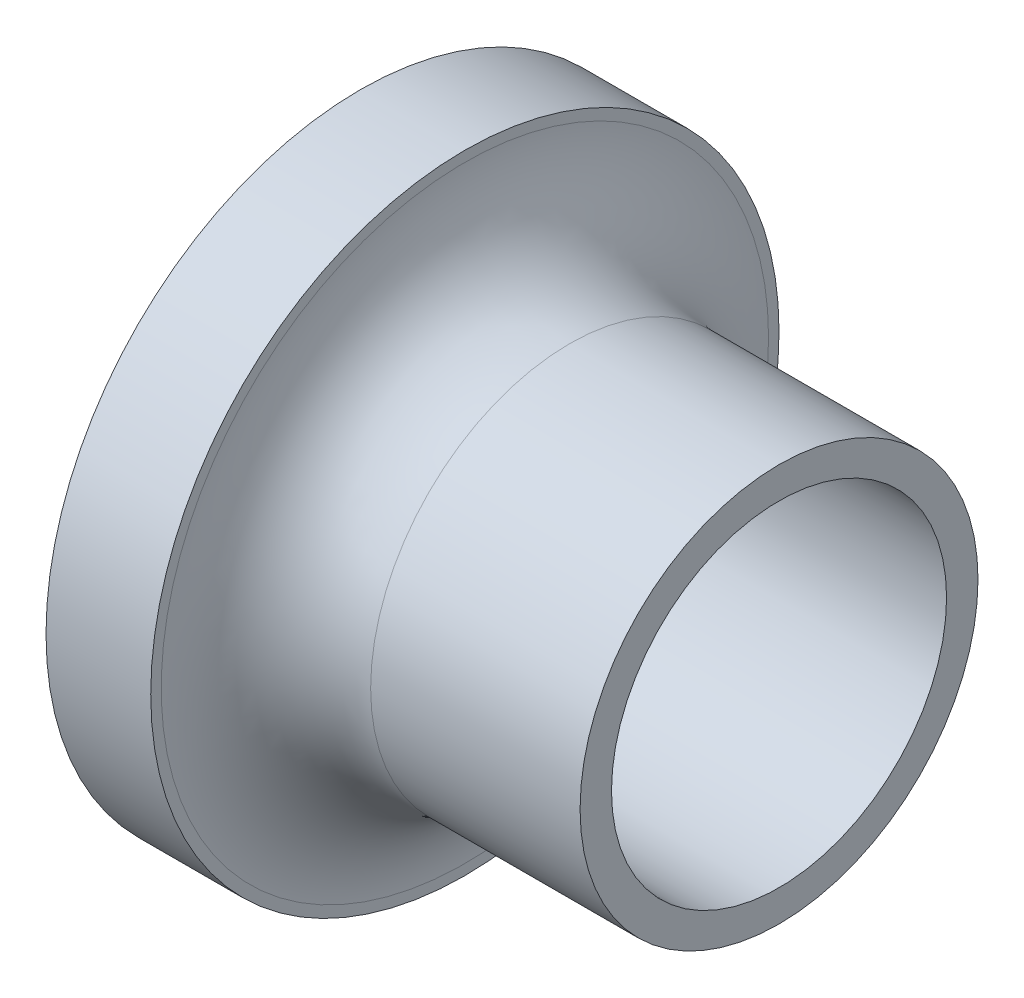
SolidWorks part; units mm, degrees
ref_plane "Piano frontale" through (0, 0, 0) normal (0, 0, 1) x (1, 0, 0)
ref_plane "Piano superiore" through (0, 0, 0) normal (0, 1, 0) x (1, 0, 0)
ref_plane "Piano destro" through (0, 0, 0) normal (1, 0, 0) x (0, 0, -1)
sketch "Schizzo1" plane through (0, 0, 0) normal (1, 0, 0) x (0, 0, -1)
  circle A0 centre (0, 0) radius 9.5
  circle A1 centre (0, 0) radius 8
  dimension "D1" = 16
  dimension "D2" = 19
extrude "Estrusione-Estrusione1" add sketch "Schizzo1" along normal blind 20
sketch "Schizzo2" plane through (0, 0, 0) normal (1, 0, 0) x (0, 0, -1)
  circle A0 centre (0, 0) radius 15
  dimension "D1" = 30
extrude "Estrusione-Estrusione2" add sketch "Schizzo2" along normal blind 5
fillet "Raccordo1" radius 5 1 edges at (5, 0, -9.5)
